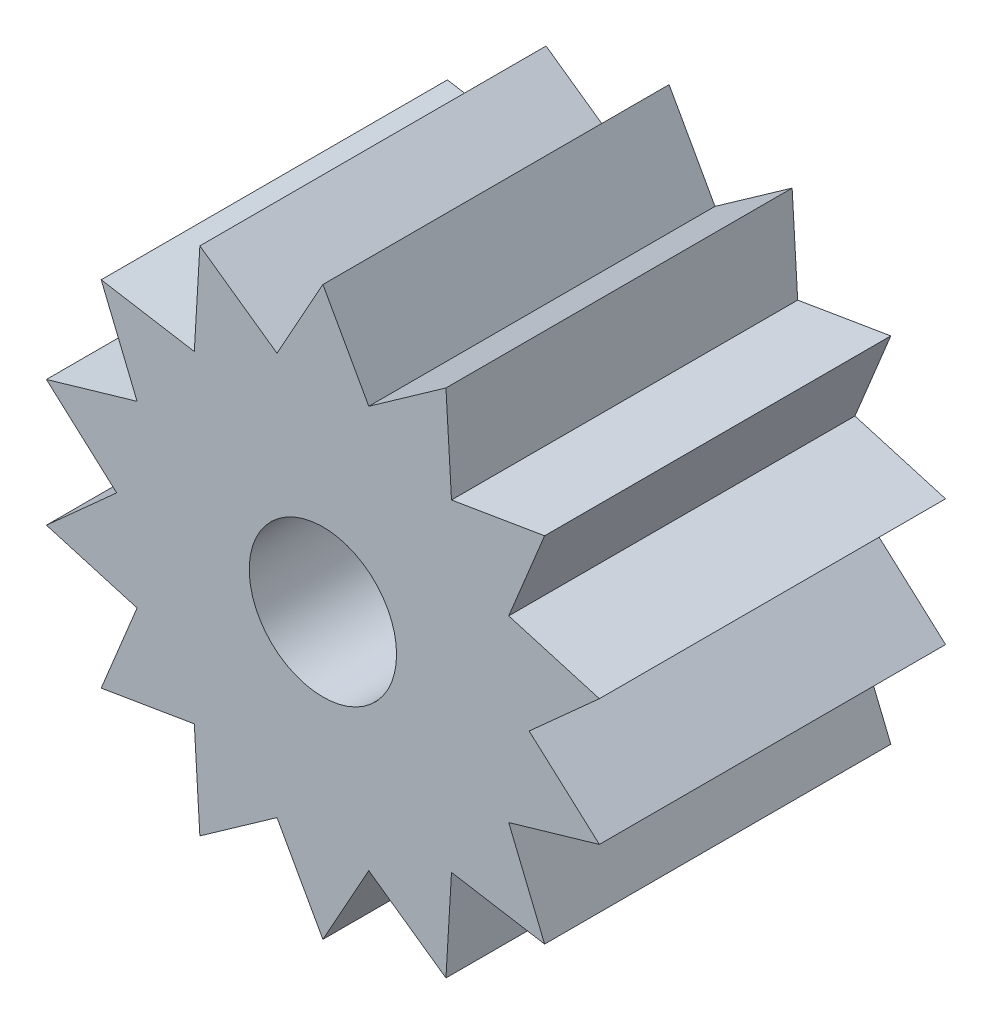
SolidWorks part; units mm, degrees
ref_plane "Front Plane" through (0, 0, 0) normal (0, 0, 1) x (1, 0, 0)
ref_plane "Top Plane" through (0, 0, 0) normal (0, 1, 0) x (1, 0, 0)
ref_plane "Right Plane" through (0, 0, 0) normal (1, 0, 0) x (0, 0, -1)
sketch "Sketch1" plane through (0, 0, 0) normal (0, 0, 1) x (1, 0, 0)
  line L0 (0, 3.85) -> (0.6231, 2.7298)
  line L1 (0.6231, 2.7298) -> (1.6705, 3.4687)
  line L2 (1.6705, 3.4687) -> (1.7458, 2.1891)
  line L3 (1.7458, 2.1891) -> (3.0101, 2.4004)
  line L4 (3.0101, 2.4004) -> (2.5227, 1.2149)
  line L5 (2.5227, 1.2149) -> (3.7535, 0.8567)
  line L6 (3.7535, 0.8567) -> (2.8, 0)
  line L7 (2.8, 0) -> (3.7535, -0.8567)
  line L8 (3.7535, -0.8567) -> (2.5227, -1.2149)
  line L9 (2.5227, -1.2149) -> (3.0101, -2.4004)
  line L10 (3.0101, -2.4004) -> (1.7458, -2.1891)
  line L11 (1.7458, -2.1891) -> (1.6705, -3.4687)
  line L12 (1.6705, -3.4687) -> (0.6231, -2.7298)
  line L13 (0.6231, -2.7298) -> (0, -3.85)
  line L14 (0, -3.85) -> (-0.6231, -2.7298)
  line L15 (-0.6231, -2.7298) -> (-1.6705, -3.4687)
  line L16 (-1.6705, -3.4687) -> (-1.7458, -2.1891)
  line L17 (-1.7458, -2.1891) -> (-3.0101, -2.4004)
  line L18 (-3.0101, -2.4004) -> (-2.5227, -1.2149)
  line L19 (-2.5227, -1.2149) -> (-3.7535, -0.8567)
  line L20 (-3.7535, -0.8567) -> (-2.8, 0)
  line L21 (-2.8, 0) -> (-3.7535, 0.8567)
  line L22 (-3.7535, 0.8567) -> (-2.5227, 1.2149)
  line L23 (-2.5227, 1.2149) -> (-3.0101, 2.4004)
  line L24 (-3.0101, 2.4004) -> (-1.7458, 2.1891)
  line L25 (-1.7458, 2.1891) -> (-1.6705, 3.4687)
  line L26 (-1.6705, 3.4687) -> (-0.6231, 2.7298)
  line L27 (-0.6231, 2.7298) -> (0, 3.85)
  circle A1 centre (0, 0) radius 1
  point P21 (0, 0)
  point P48 (0, 0)
  dimension "D1" = 14
  dimension "D2" = 2
extrude "Boss-Extrude1" add sketch "Sketch1" along normal blind 4.7
